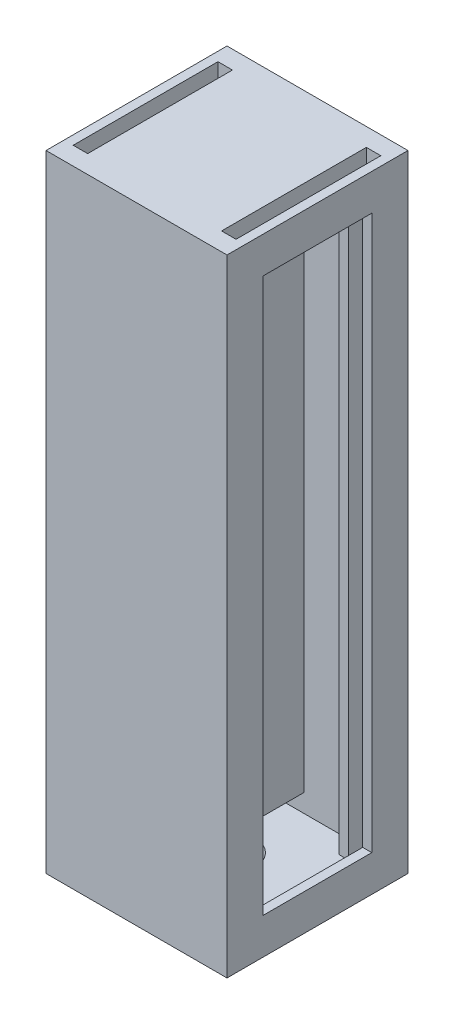
SolidWorks part; units mm, degrees
ref_plane "Front Plane" through (0, 0, 0) normal (0, 0, 1) x (1, 0, 0)
ref_plane "Top Plane" through (0, 0, 0) normal (0, 1, 0) x (1, 0, 0)
ref_plane "Right Plane" through (0, 0, 0) normal (1, 0, 0) x (0, 0, -1)
sketch "Sketch1" plane through (0, 0, 0) normal (0, 1, 0) x (1, 0, 0)
  line L1 (-15.875, 15.875) -> (15.875, 15.875)
  line L2 (-15.875, 15.875) -> (-15.875, -15.875)
  line L3 (-15.875, -15.875) -> (15.875, -15.875)
  line L4 (15.875, 15.875) -> (15.875, -15.875)
  line L5 (-15.875, 15.875) -> (15.875, -15.875) construction
  line L6 (-15.875, -15.875) -> (15.875, 15.875) construction
  point P0 (0, 0)
  dimension "D1" = 31.75
  dimension "D2" = 31.75
extrude "Boss-Extrude1" add sketch "Sketch1" along normal blind 109.855
shell "Shell1" thickness 3.175
sketch "Sketch2" plane through (0, 0, 0) normal (0, -1, 0) x (1, 0, 0)
  circle A0 centre (0, 0) radius 4.7625
  dimension "D1" = 9.525
extrude "Cut-Extrude1" cut sketch "Sketch2" against normal up to surface (3.175 mm away) up to face at (1.5875, 3.175, 0)
sketch "Sketch4" plane through (0, 3.175, 0) normal (0, 1, 0) x (1, 0, 0)
  line L0 (-12.7, -12.7) -> (15.875, -12.7) construction
  line L1 (15.875, -12.7) -> (14.2875, -12.7)
  line L2 (15.875, -12.7) -> (15.875, -9.525)
  line L3 (15.875, -9.525) -> (14.2875, -9.525)
  line L4 (14.2875, -12.7) -> (14.2875, -9.525)
  line L5 (15.875, 12.7) -> (14.2875, 12.7)
  line L6 (15.875, 12.7) -> (15.875, 9.525)
  line L7 (15.875, 9.525) -> (14.2875, 9.525)
  line L8 (14.2875, 12.7) -> (14.2875, 9.525)
  line L9 (11.7475, -12.7) -> (10.16, -12.7)
  line L10 (11.7475, -12.7) -> (11.7475, -9.525)
  line L11 (11.7475, -9.525) -> (10.16, -9.525)
  line L12 (10.16, -12.7) -> (10.16, -9.525)
  line L13 (15.875, 12.7) -> (-12.7, 12.7) construction
  line L14 (11.7475, 12.7) -> (10.16, 12.7)
  line L15 (11.7475, 12.7) -> (11.7475, 9.525)
  line L16 (11.7475, 9.525) -> (10.16, 9.525)
  line L17 (10.16, 12.7) -> (10.16, 9.525)
  line L18 (0, 0) -> (0, 4.655) construction
  line L19 (-11.7475, 12.7) -> (-10.16, 12.7)
  line L20 (-15.875, 12.7) -> (-14.2875, 12.7)
  line L21 (-15.875, 12.7) -> (-15.875, 9.525)
  line L22 (-15.875, 9.525) -> (-14.2875, 9.525)
  line L23 (-14.2875, 12.7) -> (-14.2875, 9.525)
  line L24 (-11.7475, 12.7) -> (-11.7475, 9.525)
  line L25 (-11.7475, 9.525) -> (-10.16, 9.525)
  line L26 (-10.16, 12.7) -> (-10.16, 9.525)
  line L27 (-15.875, -12.7) -> (-15.875, -9.525)
  line L28 (-15.875, -9.525) -> (-14.2875, -9.525)
  line L29 (-14.2875, -12.7) -> (-14.2875, -9.525)
  line L30 (-15.875, -12.7) -> (-14.2875, -12.7)
  line L31 (-11.7475, -12.7) -> (-11.7475, -9.525)
  line L32 (-11.7475, -12.7) -> (-10.16, -12.7)
  line L33 (-11.7475, -9.525) -> (-10.16, -9.525)
  line L34 (-10.16, -12.7) -> (-10.16, -9.525)
  dimension "D1" = 1.5875
  dimension "D2" = 3.175
  dimension "D3" = 2.54
  dimension "D4" = 2.54
sketch "Sketch5" plane through (0, 3.175, 0) normal (0, 1, 0) x (1, 0, 0)
  line L0 (0, 0) -> (0, 3.95) construction
  line L1 (11.7475, -12.7) -> (14.2875, -12.7)
  line L2 (11.7475, -12.7) -> (11.7475, 12.7)
  line L3 (11.7475, 12.7) -> (14.2875, 12.7)
  line L4 (14.2875, -12.7) -> (14.2875, 12.7)
  line L5 (-11.7475, 12.7) -> (-14.2875, 12.7)
  line L6 (-11.7475, -12.7) -> (-11.7475, 12.7)
  line L7 (-11.7475, -12.7) -> (-14.2875, -12.7)
  line L8 (-14.2875, -12.7) -> (-14.2875, 12.7)
extrude "Boss-Extrude4" add sketch "Sketch4" along normal up to surface (103.505 mm away) up to face at (1.5875, 106.68, 0)
sketch "Sketch6" plane through (-12.7, 0, 0) normal (1, 0, 0) x (0, 0, -1)
  line L1 (-9.525, 106.68) -> (9.525, 106.68)
  line L2 (-9.525, 106.68) -> (-9.525, 3.175)
  line L3 (-9.525, 3.175) -> (9.525, 3.175)
  line L4 (9.525, 106.68) -> (9.525, 3.175)
extrude "Cut-Extrude3" cut sketch "Sketch6" against normal blind 114.3
extrude "Cut-Extrude2" cut sketch "Sketch5" along normal up to surface (106.68 mm away) up to face at (0, 109.855, 0)
sketch "Sketch8" plane through (15.875, 0, 0) normal (1, 0, 0) x (0, 0, -1)
  line L0 (9.525, 106.68) -> (9.525, 3.175) construction
  line L1 (-9.525, 106.68) -> (9.525, 106.68)
  line L2 (-9.525, 106.68) -> (-9.525, 103.505)
  line L3 (-9.525, 103.505) -> (9.525, 103.505)
  line L4 (9.525, 106.68) -> (9.525, 103.505)
  line L5 (-9.525, 54.9275) -> (9.525, 54.9275) construction
  line L6 (-9.525, 106.68) -> (-9.525, 3.175) construction
  line L7 (9.525, 3.175) -> (9.525, 6.35)
  line L8 (-9.525, 3.175) -> (9.525, 3.175)
  line L9 (-9.525, 3.175) -> (-9.525, 6.35)
  line L10 (-9.525, 6.35) -> (9.525, 6.35)
  dimension "D1" = 3.175
extrude "Boss-Extrude5" add sketch "Sketch8" against normal up to surface (1.5875 mm away) up to face at (14.2875, 55.7213, 0)
sketch "Sketch10" plane through (-15.875, 0, 0) normal (-1, 0, 0) x (0, 0, 1)
  line L12 (-9.525, 6.35) -> (-9.525, 3.175)
  line L13 (9.525, 6.35) -> (-9.525, 6.35)
  line L14 (9.525, 3.175) -> (9.525, 6.35)
  line L15 (-9.525, 3.175) -> (9.525, 3.175)
  line L16 (-9.525, 6.35) -> (-9.525, 3.175)
  line L17 (9.525, 6.35) -> (-9.525, 6.35)
  line L18 (9.525, 3.175) -> (9.525, 6.35)
  line L19 (-9.525, 3.175) -> (9.525, 3.175)
  line L20 (9.525, 106.68) -> (-9.525, 106.68)
  line L21 (-9.525, 106.68) -> (-9.525, 103.505)
  line L22 (-9.525, 103.505) -> (9.525, 103.505)
  line L23 (9.525, 103.505) -> (9.525, 106.68)
  line L24 (9.525, 106.68) -> (-9.525, 106.68)
  line L25 (-9.525, 106.68) -> (-9.525, 103.505)
  line L26 (-9.525, 103.505) -> (9.525, 103.505)
  line L27 (9.525, 103.505) -> (9.525, 106.68)
  dimension "D2" = 0
  dimension "D3" = 0
extrude "Boss-Extrude7" add sketch "Sketch10" against normal up to surface (1.5875 mm away) up to face at (-14.2875, 55.7213, 0)
sketch "Sketch11" plane through (0, 109.855, 0) normal (0, 1, 0) x (1, 0, 0)
  line L0 (-15.875, -15.875) -> (15.875, -15.875) construction
  line L1 (0.7938, 15.875) -> (-0.7937, 15.875)
  line L2 (0.7938, 15.875) -> (0.7938, -15.875)
  line L3 (0.7938, -15.875) -> (-0.7937, -15.875)
  line L4 (-0.7937, 15.875) -> (-0.7937, -15.875)
  line L5 (0.7938, 15.875) -> (-0.7937, -15.875) construction
  line L6 (0.7938, -15.875) -> (-0.7937, 15.875) construction
  point P0 (0, 0)
  dimension "D1" = 1.5875
extrude "Boss-Extrude8" add sketch "Sketch11" against normal up to surface (103.505 mm away) up to face at (-15.0812, 6.35, 0)
sketch "Sketch13" plane through (0, 0, 0) normal (0, -1, 0) x (1, 0, 0)
  circle A0 centre (0, 0) radius 4.7625
  circle A1 centre (0, 0) radius 6.35
  dimension "D1" = 12.7
extrude "Boss-Extrude9" add sketch "Sketch13" along normal blind 9.525
